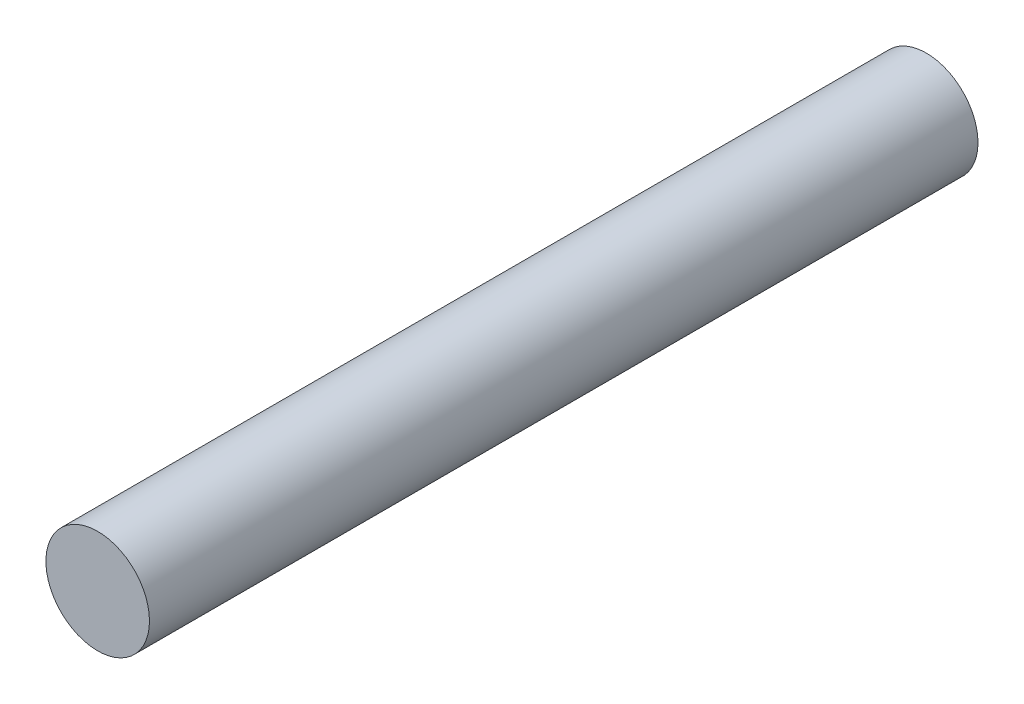
SolidWorks part; units mm, degrees
ref_plane "Front Plane" through (0, 0, 0) normal (0, 0, 1) x (1, 0, 0)
ref_plane "Top Plane" through (0, 0, 0) normal (0, 1, 0) x (1, 0, 0)
ref_plane "Right Plane" through (0, 0, 0) normal (1, 0, 0) x (0, 0, -1)
sketch "Sketch1" plane through (0, 0, 0) normal (0, 0, 1) x (1, 0, 0)
  circle A0 centre (0, 0) radius 1
  dimension "D1" = 2
extrude "Boss-Extrude1" add sketch "Sketch1" along normal blind 16
ref_plane "Plane1" through (0, 0, 8) normal (0, 0, 1) x (1, 0, 0)
